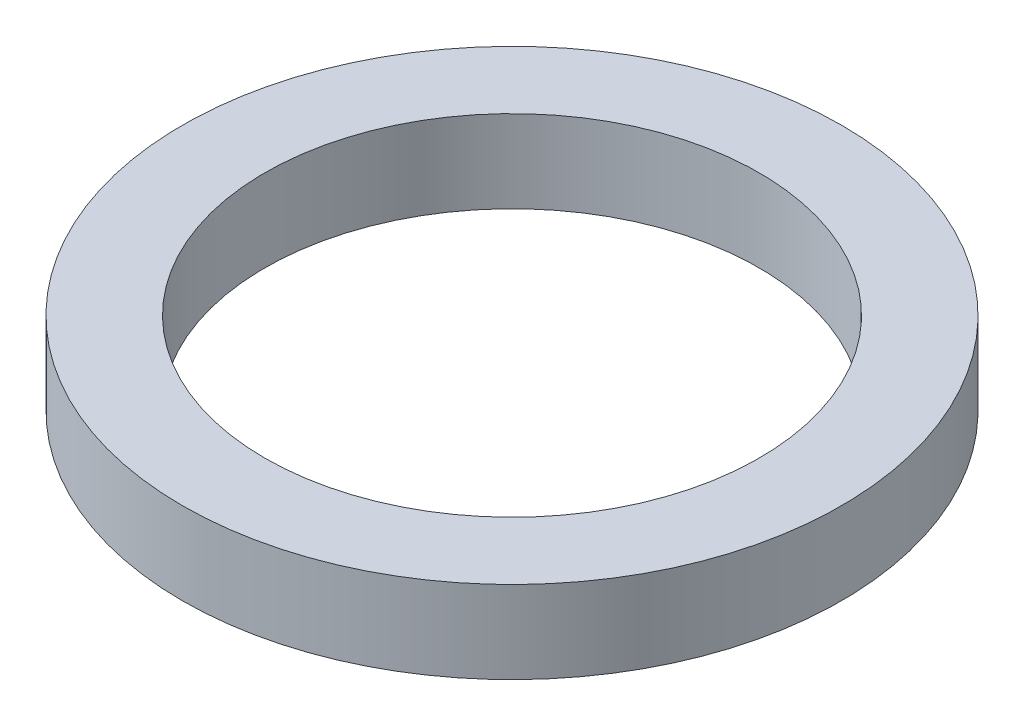
SolidWorks part; units mm, degrees
material "Nylon 6/10"
ref_plane "Front Plane" through (0, 0, 0) normal (0, 0, 1) x (1, 0, 0)
ref_plane "Top Plane" through (0, 0, 0) normal (0, 1, 0) x (1, 0, 0)
ref_plane "Right Plane" through (0, 0, 0) normal (1, 0, 0) x (0, 0, -1)
sketch "Sketch1" plane through (0, 0, 0) normal (1, 0, 0) x (0, 0, -1)
  line L0 (0, 10.073) -> (0, -9.4161) construction
  line L2 (3, 0.5) -> (4, 0.5)
  line L3 (3, 0.5) -> (3, -0.5)
  line L4 (3, -0.5) -> (4, -0.5)
  line L5 (4, 0.5) -> (4, -0.5)
  point P7 (3, 0)
  dimension "D1" = 6
  dimension "D2" = 8
  dimension "D3" = 1
revolve "Revolve1" add sketch "Sketch1" angle 360 about L0
